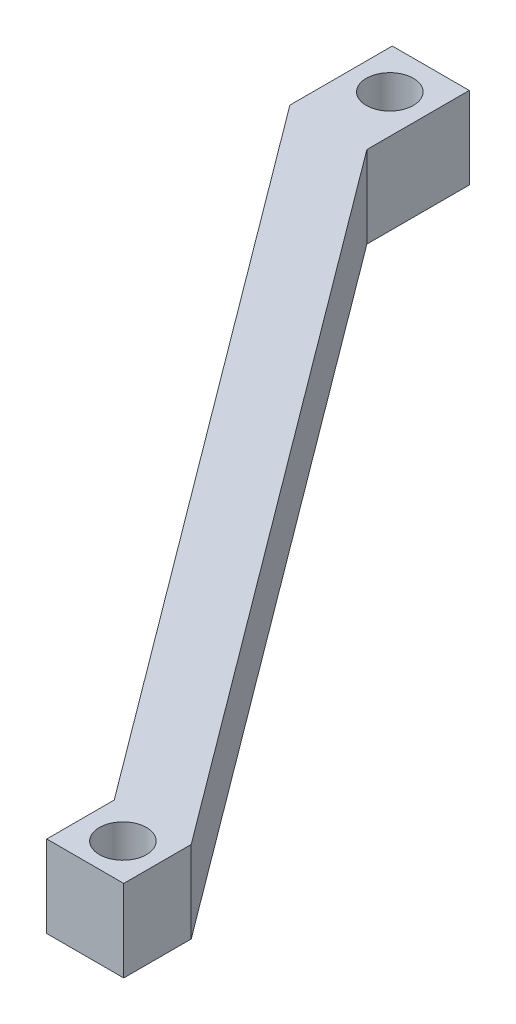
SolidWorks part; units mm, degrees
ref_plane "Front Plane" through (0, 0, 0) normal (0, 0, 1) x (1, 0, 0)
ref_plane "Top Plane" through (0, 0, 0) normal (0, 1, 0) x (1, 0, 0)
ref_plane "Right Plane" through (0, 0, 0) normal (1, 0, 0) x (0, 0, -1)
sketch "Sketch2" plane through (0, 0, 0) normal (0, 1, 0) x (1, 0, 0)
  line L0 (0, 0) -> (127.8067, -189.6794) construction
  line L1 (9.3969, 10) -> (9.3969, -15)
  line L2 (9.3969, -15) -> (134.8871, -183.3812)
  line L3 (134.8871, -183.3812) -> (134.8871, -199.8559)
  line L4 (134.8871, -199.8559) -> (116.0933, -199.8559)
  line L5 (116.0933, -199.8559) -> (116.0933, -183.3812)
  line L6 (116.0933, -183.3812) -> (-9.3969, -15)
  line L7 (-9.3969, -15) -> (-9.3969, 10)
  line L8 (-9.3969, 10) -> (9.3969, 10)
  point P5 (0, 10)
  point P12 (0, 0)
  point P13 (135.5722, -182.2316)
  dimension "D1" = 228.72
  dimension "D2" = 25
  dimension "D3" = 15
  dimension "D4" = 210
extrude "Boss-Extrude2" add sketch "Sketch2" along normal blind 20
sketch "Sketch3" plane through (0, 20, 0) normal (0, 1, 0) x (1, 0, 0)
  circle A0 centre (0, 0) radius 5.75
  circle A1 centre (125.8347, -190.9933) radius 5.75
  dimension "D1" = 11.5
  dimension "D2" = 11.5
  dimension "D3" = 228.72
extrude "Cut-Extrude1" cut sketch "Sketch3" against normal through all
